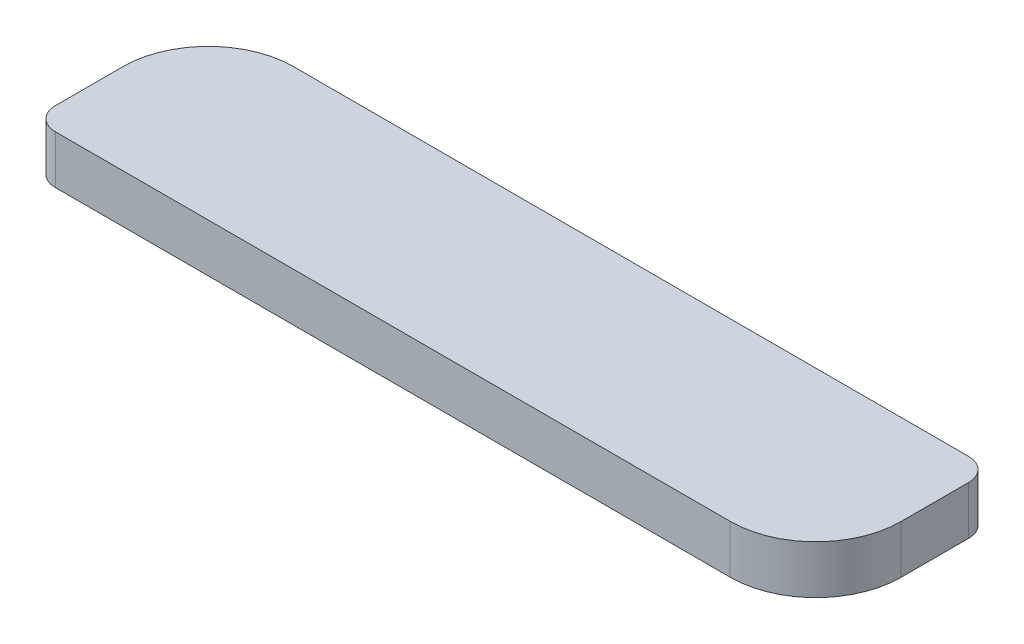
SolidWorks part; units mm, degrees
ref_plane "Front Plane" through (0, 0, 0) normal (0, 0, 1) x (1, 0, 0)
ref_plane "Top Plane" through (0, 0, 0) normal (0, 1, 0) x (1, 0, 0)
ref_plane "Right Plane" through (0, 0, 0) normal (1, 0, 0) x (0, 0, -1)
sketch "Sketch1" plane through (0, 0, 0) normal (0, 1, 0) x (1, 0, 0)
  line L0 (0, 0) -> (300, 0)
  line L1 (338, 38) -> (338, 68)
  line L2 (328, 78) -> (28, 78)
  line L3 (-10, 40) -> (-10, 10)
  arc A0 (300, 0) -> (338, 38) centre (300, 38) ccw
  arc A1 (338, 68) -> (328, 78) centre (328, 68) ccw
  arc A2 (0, 0) -> (-10, 10) centre (0, 10) cw
  arc A3 (28, 78) -> (-10, 40) centre (28, 40) ccw
  dimension "D2" = 38
  dimension "D4" = 10
  dimension "D6" = 10
  dimension "D7" = 38
  dimension "D1" = 300
  dimension "D3" = 30
  dimension "D5" = 300
extrude "Boss-Extrude2" add sketch "Sketch1" along normal blind 21.5
ref_plane "Plane2" through (28, 0, 0) normal (1, 0, 0) x (0, 0, -1)
sketch "Sketch5" plane through (28, 0, 0) normal (1, 0, 0) x (0, 0, -1)
  line L0 (78, 0) -> (42, 0)
  line L1 (38, 0) -> (68, 0) construction
  line L2 (78, 0) -> (78, -8.17)
  line L3 (78, -8.17) -> (75.1716, -10.9984)
  line L4 (75.1716, -10.9984) -> (72.3416, -10.9984)
  line L5 (60, 0) -> (60, -21.5041) construction
  line L6 (44.8284, -10.9984) -> (47.6584, -10.9984)
  line L7 (42, -8.17) -> (44.8284, -10.9984)
  line L8 (42, 0) -> (42, -8.17)
  arc A0 (47.6584, -10.9984) -> (72.3416, -10.9984) centre (60, -12.9823) cw
  dimension "D6" = 12.5
  dimension "D1" = 36
  dimension "D2" = 8.17
  dimension "D3" = 135
  dimension "D4" = 4
  dimension "D5" = 2.83
extrude "Boss-Extrude3" add sketch "Sketch5" along normal blind 266
